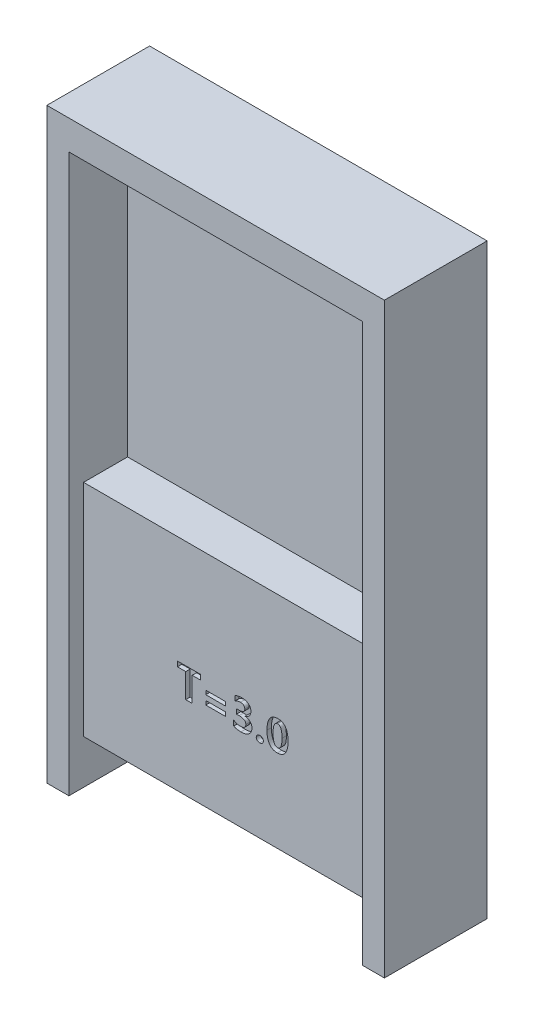
SolidWorks part; units mm, degrees
ref_plane "前视基准面" through (0, 0, 0) normal (0, 0, 1) x (1, 0, 0)
ref_plane "上视基准面" through (0, 0, 0) normal (0, 1, 0) x (1, 0, 0)
ref_plane "右视基准面" through (0, 0, 0) normal (1, 0, 0) x (0, 0, -1)
sketch "草图1" plane through (0, 0, 0) normal (0, 0, 1) x (1, 0, 0)
  line L0 (-1020, 0) -> (-11.5, 0) construction
  line L1 (0, 0) -> (0, 25.9672) construction
  line L2 (-10, 0) -> (-10, -18)
  line L4 (-10, 0) -> (-10, 20)
  line L5 (-10, 20) -> (10, 20)
  line L6 (10, 0) -> (10, 20)
  line L8 (10, -18) -> (10, 0)
  line L10 (-11.5, 22) -> (11.5, 22)
  line L11 (-11.5, 22) -> (-11.5, -18)
  line L12 (-11.5, -18) -> (-10, -18)
  line L13 (11.5, 22) -> (11.5, -18)
  line L15 (10, -18) -> (11.5, -18)
  line L16 (11.5, 0) -> (1020.3279, 0) construction
  point P2 (0, 20)
  point P16 (0, 22)
  point P21 (0, 0)
  point P22 (0, 0)
  point P23 (0, 0)
  point P24 (0, 0)
  dimension "D1" = 20
  dimension "D2" = 20
  dimension "D4" = 23
  dimension "D5" = 40
  dimension "D6" = 22
extrude "凸台-拉伸1" add sketch "草图1" along normal blind 7
sketch "草图2" plane through (0, 0, 0) normal (0, 0, 1) x (1, 0, 0)
  line L0 (0, 0) -> (32.0423, 0) construction
  line L1 (10, 20) -> (10, -18) construction
  line L2 (0, 0) -> (0, 18.5674) construction
  line L3 (-10, 20) -> (10, 20)
  line L4 (-10, 20) -> (-10, -15)
  line L5 (-10, -15) -> (10, -15)
  line L6 (10, 20) -> (10, -15)
  dimension "D1" = 35
extrude "凸台-拉伸2" add sketch "草图2" along normal blind 6
sketch "草图3" plane through (0, 0, 6) normal (0, 0, 1) x (1, 0, 0)
  line L0 (-10, 0) -> (10, 0)
  line L1 (-10, 20) -> (-10, -15) construction
  line L2 (10, -15) -> (10, 20) construction
  line L3 (-10, 0) -> (-10, 20)
  line L4 (-10, 20) -> (10, 20)
  line L5 (10, 20) -> (10, 0)
extrude "切除-拉伸1" cut sketch "草图3" against normal blind 3
sketch "草图4" plane through (0, 0, 0) normal (0, 0, -1) x (-1, 0, 0)
  line L0 (0, 0) -> (0, 18.3654) construction
  line L1 (-7, -2) -> (7, -2)
  line L2 (-7, -2) -> (-7, -12)
  line L3 (-7, -12) -> (7, -12)
  line L4 (7, -2) -> (7, -12)
  line L5 (10, -15) -> (-10, -15) construction
  line L6 (10, 0) -> (-10, 0) construction
  point P5 (0, -2)
  dimension "D1" = 2
  dimension "D2" = 14
  dimension "D3" = 3
extrude "切除-拉伸2" cut sketch "草图4" against normal blind 5
sketch "草图5" plane through (0, 0, 6) normal (0, 0, 1) x (1, 0, 0)
  text T0 "T=3.0" font "微软雅黑" height 2
extrude "切除-拉伸3" cut sketch "草图5" against normal blind 0.3
